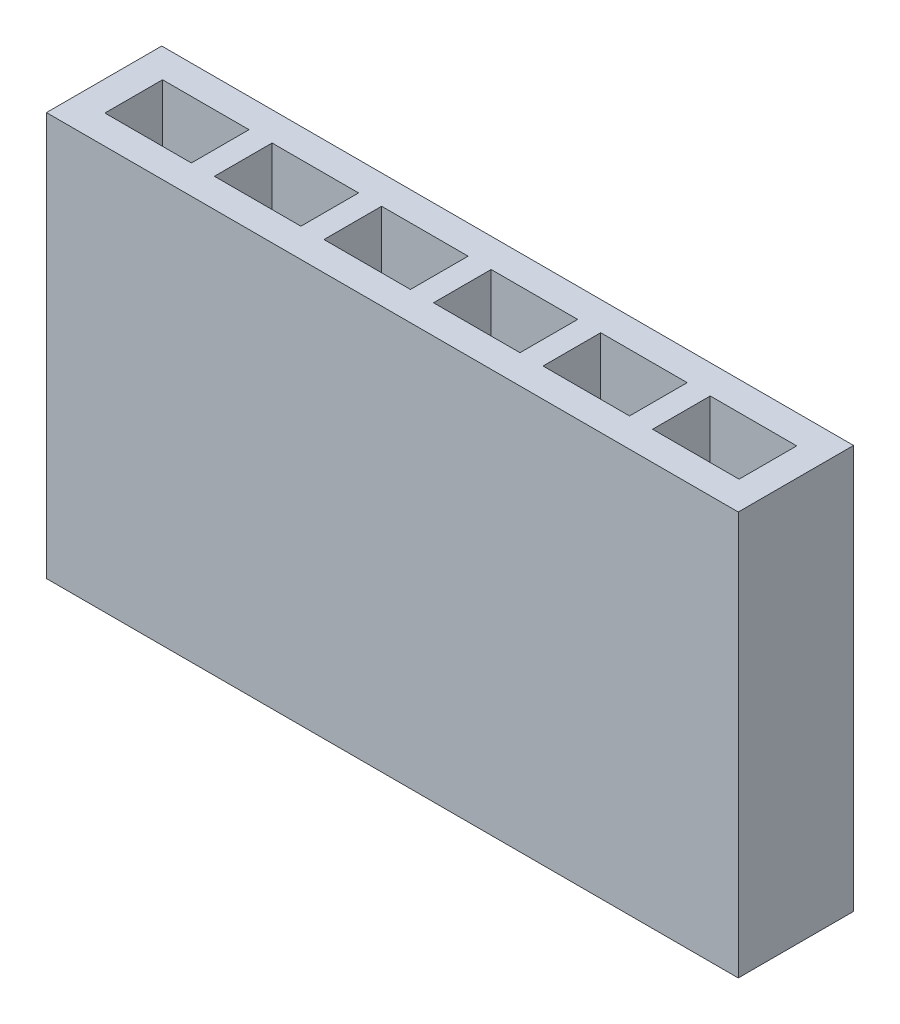
SolidWorks part; units mm, degrees
ref_plane "Front Plane" through (0, 0, 0) normal (0, 0, 1) x (1, 0, 0)
ref_plane "Top Plane" through (0, 0, 0) normal (0, 1, 0) x (1, 0, 0)
ref_plane "Right Plane" through (0, 0, 0) normal (1, 0, 0) x (0, 0, -1)
sketch "Sketch1" plane through (0, 0, 0) normal (0, 0, 1) x (1, 0, 0)
  line L1 (0, 0) -> (12, 0)
  line L2 (0, 0) -> (0, 7)
  line L3 (0, 7) -> (12, 7)
  line L4 (12, 0) -> (12, 7)
  dimension "D1" = 12
  dimension "D2" = 7
extrude "Boss-Extrude1" add sketch "Sketch1" along normal blind 2
sketch "Sketch3" plane through (0, 7, 0) normal (0, 1, 0) x (1, 0, 0)
  line L0 (0, -1) -> (12, -1) construction
  line L1 (0, -2) -> (0, 0) construction
  line L2 (12, -2) -> (12, 0) construction
  line L4 (0.5139, -0.5) -> (2.0139, -0.5)
  line L5 (0.5139, -0.5) -> (0.5139, -1.5)
  line L6 (0.5139, -1.5) -> (2.0139, -1.5)
  line L7 (2.0139, -0.5) -> (2.0139, -1.5)
  dimension "D1" = 1.5
  dimension "D2" = 1
extrude "Cut-Extrude1" cut sketch "Sketch3" against normal blind 4
pattern_linear "LPattern1" count 6 spacing 1.9 along (1, 0, 0) of "Cut-Extrude1"
